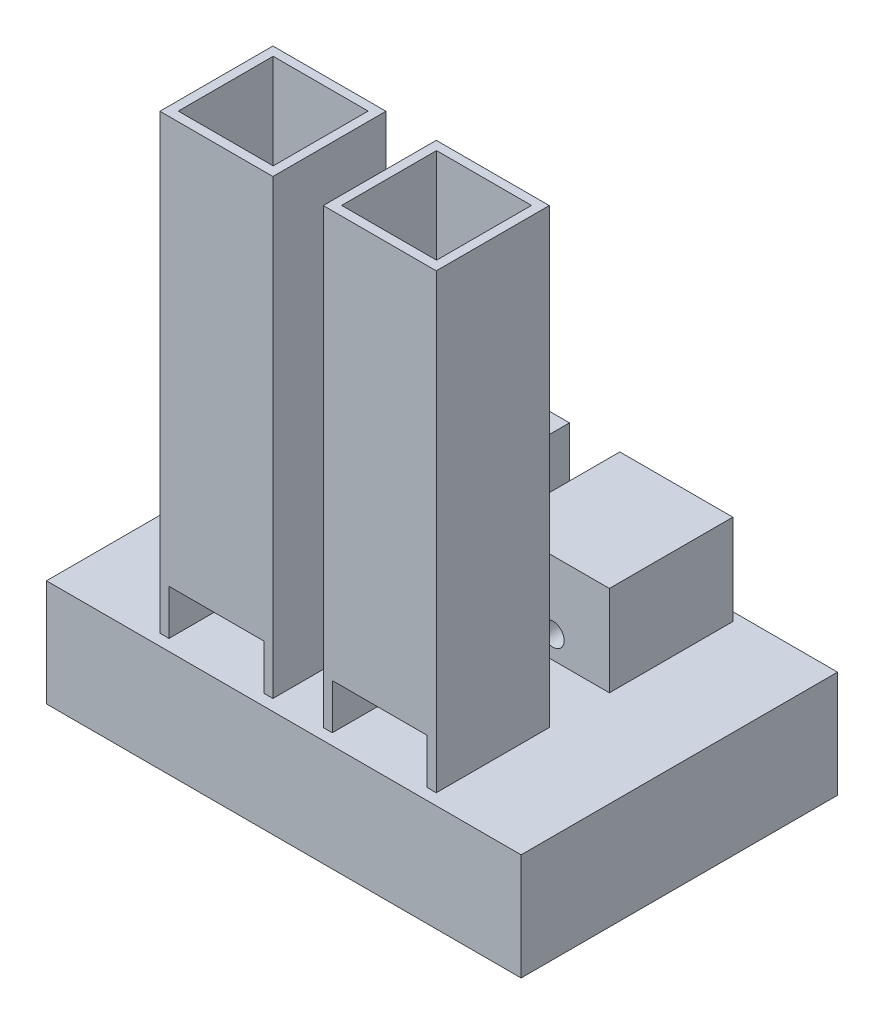
SolidWorks part; units mm, degrees
ref_plane "Front Plane" through (0, 0, 0) normal (0, 0, 1) x (1, 0, 0)
ref_plane "Top Plane" through (0, 0, 0) normal (0, 1, 0) x (1, 0, 0)
ref_plane "Right Plane" through (0, 0, 0) normal (1, 0, 0) x (0, 0, -1)
sketch "Sketch1" plane through (0, 0, 0) normal (0, 1, 0) x (1, 0, 0)
  line L1 (0, 0) -> (266.7, 0)
  line L2 (0, 0) -> (0, 177.8)
  line L3 (0, 177.8) -> (266.7, 177.8)
  line L4 (266.7, 0) -> (266.7, 177.8)
  dimension "D1" = 266.7
  dimension "D2" = 177.8
extrude "Boss-Extrude1" add sketch "Sketch1" along normal blind 59.944
sketch "Sketch2" plane through (0, 59.944, 0) normal (0, 1, 0) x (1, 0, 0)
  line L1 (149.178, 69.85) -> (212.678, 69.85)
  line L2 (149.178, 69.85) -> (149.178, 6.35)
  line L3 (149.178, 6.35) -> (212.678, 6.35)
  line L4 (212.678, 69.85) -> (212.678, 6.35)
  line L8 (0, 0) -> (266.7, 0) construction
  line L9 (57.3904, 69.85) -> (120.8904, 69.85)
  line L10 (154.258, 64.9303) -> (207.598, 64.9303)
  line L11 (154.258, 64.9303) -> (154.258, 11.5903)
  line L12 (154.258, 11.5903) -> (207.598, 11.5903)
  line L13 (207.598, 64.9303) -> (207.598, 11.5903)
  line L14 (57.3904, 69.85) -> (57.3904, 6.35)
  line L15 (57.3904, 6.35) -> (120.8904, 6.35)
  line L16 (120.8904, 69.85) -> (120.8904, 6.35)
  line L17 (62.4704, 64.9303) -> (115.8104, 64.9303)
  line L18 (62.4704, 64.9303) -> (62.4704, 11.5903)
  line L19 (62.4704, 11.5903) -> (115.8104, 11.5903)
  line L20 (115.8104, 64.9303) -> (115.8104, 11.5903)
  dimension "D1" = 63.5
  dimension "D2" = 63.5
  dimension "D3" = 63.5
  dimension "D4" = 6.35
  dimension "D5" = 53.34
  dimension "D6" = 53.34
  dimension "D7" = 5.08
  dimension "D8" = 63.5
  dimension "D9" = 53.34
  dimension "D10" = 53.34
  dimension "D11" = 5.08
  dimension "D12" = 6.35
extrude "Boss-Extrude2" add sketch "Sketch2" along normal blind 254 contours L9 L16 L15 L14 | L2 L1 L4 L3 | L11 L10 L13 L12 | L17 L20 L19 L18
sketch "Sketch3" plane through (0, 0, -6.35) normal (0, 0, 1) x (1, 0, 0)
  line L0 (57.3904, 59.944) -> (120.8904, 59.944) construction
  line L1 (62.4704, 85.344) -> (115.8104, 85.344)
  line L2 (62.4704, 85.344) -> (62.4704, 59.944)
  line L3 (62.4704, 59.944) -> (115.8104, 59.944)
  line L4 (115.8104, 85.344) -> (115.8104, 59.944)
  line L5 (149.178, 59.944) -> (212.678, 59.944) construction
  line L6 (154.258, 85.344) -> (207.598, 85.344)
  line L7 (154.258, 85.344) -> (154.258, 59.944)
  line L8 (154.258, 59.944) -> (207.598, 59.944)
  line L9 (207.598, 85.344) -> (207.598, 59.944)
  line L10 (57.3904, 313.944) -> (57.3904, 59.944) construction
  line L11 (120.8904, 313.944) -> (120.8904, 59.944) construction
  line L12 (149.178, 313.944) -> (149.178, 59.944) construction
  line L13 (212.678, 313.944) -> (212.678, 59.944) construction
  dimension "D1" = 5.08
  dimension "D2" = 5.08
  dimension "D3" = 25.4
  dimension "D4" = 5.08
  dimension "D5" = 5.08
  dimension "D6" = 25.4
extrude "Cut-Extrude1" cut sketch "Sketch3" against normal blind 254
sketch "Sketch4" plane through (0, 59.944, 0) normal (0, 1, 0) x (1, 0, 0)
  line L1 (57.3904, 172.9931) -> (120.8904, 172.9931)
  line L2 (57.3904, 172.9931) -> (57.3904, 103.6199)
  line L3 (57.3904, 103.6199) -> (120.8904, 103.6199)
  line L4 (120.8904, 172.9931) -> (120.8904, 103.6199)
  line L5 (149.178, 172.9931) -> (212.678, 172.9931)
  line L6 (149.178, 172.9931) -> (149.178, 103.6199)
  line L7 (149.178, 103.6199) -> (212.678, 103.6199)
  line L8 (212.678, 172.9931) -> (212.678, 103.6199)
extrude "Boss-Extrude3" add sketch "Sketch4" along normal blind 50.8
sketch "Sketch5" plane through (0, 0, -103.6199) normal (0, 0, 1) x (1, 0, 0)
  circle A0 centre (180.928, 72.644) radius 6.35
  circle A1 centre (89.1404, 72.644) radius 6.35
  dimension "D1" = 12.7
  dimension "D2" = 12.7
extrude "Cut-Extrude2" cut sketch "Sketch5" against normal blind 50.8
